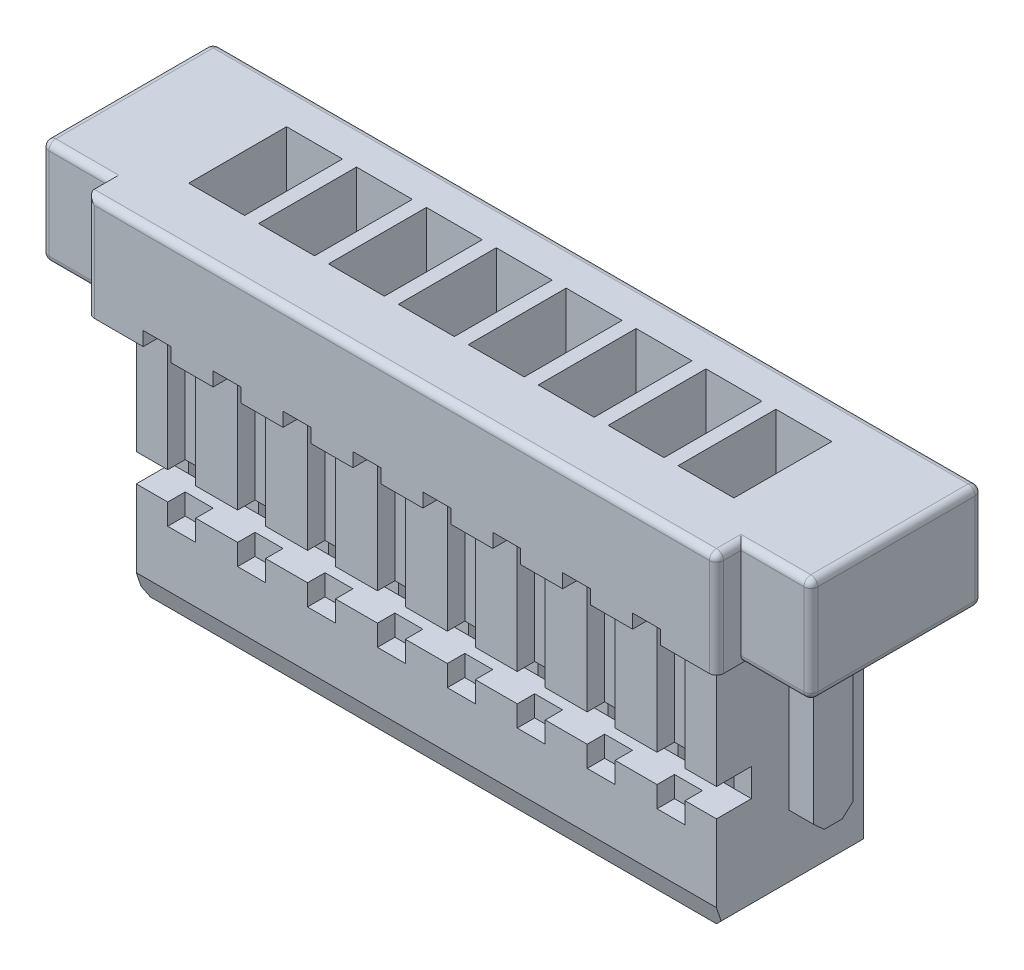
SolidWorks part; units mm, degrees
ref_plane "Front" through (0, 0, 0) normal (0, 0, 1) x (1, 0, 0)
ref_plane "Top" through (0, 0, 0) normal (0, 1, 0) x (1, 0, 0)
ref_plane "Right" through (0, 0, 0) normal (1, 0, 0) x (0, 0, -1)
sketch "Sketch1" plane through (0, 0, 0) normal (0, 0, 1) x (1, 0, 0)
  line L0 (-5.5, 1) -> (-4.5, 1)
  line L1 (5.5, 2.5) -> (-5.5, 2.5)
  line L2 (5.5, 2.5) -> (5.5, 1)
  line L3 (4.5, -2.5) -> (-4.5, -2.5)
  line L4 (-5.5, 2.5) -> (-5.5, 1)
  line L7 (-4.5, 1) -> (-4.5, -2.5)
  line L8 (0, 2.2875) -> (0, 41.3139) construction
  line L9 (4.5, 1) -> (4.5, -2.5)
  line L10 (5.5, 1) -> (4.5, 1)
  point P0 (0, 0)
  dimension "D1" = 11
  dimension "D2" = 5
  dimension "D3" = 9
  dimension "D4" = 1.5
extrude "Extrude1" add sketch "Sketch1" along normal blind 2.8
sketch "Sketch2" plane through (0, 0, 0) normal (1, 0, 0) x (0, 0, -1)
  line L0 (-2.45, 1) -> (-2.45, -2.5)
  line L1 (-0.35, 1) -> (-0.35, -2.5)
  line L2 (0, -2.5) -> (0, 1) construction
  line L3 (-2.8, -2.5) -> (-2.8, 1) construction
  line L4 (-2.8, -2.5) -> (0, -2.5) construction
  line L5 (-2.8, 1) -> (0, 1) construction
  line L6 (0, -2.5) -> (0, 1)
  line L7 (-2.8, -2.5) -> (-2.8, 1)
  line L8 (-2.8, -2.5) -> (-2.45, -2.5)
  line L9 (-2.8, 1) -> (-2.45, 1)
  line L10 (-0.35, 1) -> (0, 1)
  line L11 (-0.35, -2.5) -> (0, -2.5)
  dimension "D1" = 2.1
  dimension "D2" = 0.35
extrude "Extrude2" cut sketch "Sketch2" against normal through all and the other way through all
sketch "Sketch3" plane through (5.5, 0, 0) normal (1, 0, 0) x (0, 0, -1)
  line L0 (-2.45, 1) -> (-2.45, 2.5)
  line L1 (-2.8, 1) -> (0, 1) construction
  line L2 (-2.45, 1) -> (-0.35, 1) construction
  line L3 (-2.8, 2.5) -> (0, 2.5) construction
  line L4 (-2.8, 1) -> (-2.8, 2.5) construction
  line L5 (-2.8, 1) -> (-2.45, 1)
  line L6 (-2.8, 1) -> (-2.8, 2.5)
  line L7 (-2.8, 2.5) -> (-2.45, 2.5)
extrude "Extrude3" cut sketch "Sketch3" along direction (-1, 0, 0) on the side against the normal blind 1
mirror "Mirror1" about plane through (0, 0, 0) normal (1, 0, 0) of "Extrude3"
sketch "Sketch4" plane through (4.5, 0, 0) normal (1, 0, 0) x (0, 0, -1)
  line L0 (-1.41, 1) -> (-1.41, -1.5131)
  line L1 (-2.45, 1) -> (0, 1) construction
  line L2 (-1.41, -1.5131) -> (-1.26, -1.65)
  line L3 (-1.26, -1.65) -> (-1, -1.65)
  line L4 (-1, -1.65) -> (-0.85, -1.5131)
  line L5 (-0.85, -1.5131) -> (-0.85, 1)
  line L6 (-2.45, 1) -> (-0.35, 1) construction
  line L7 (-0.85, 1) -> (-0.35, 1)
  line L8 (-0.35, -2.5) -> (-0.35, 1) construction
  line L9 (-2.45, -2.5) -> (-0.35, -2.5) construction
  line L10 (-2.45, 1) -> (-2.45, -2.5) construction
  line L11 (-0.35, -2.5) -> (-0.35, 1)
  line L12 (-2.45, -2.5) -> (-0.35, -2.5)
  line L13 (-2.45, 1) -> (-2.45, -2.5)
  line L14 (-2.45, 1) -> (-1.41, 1)
  line L15 (0, 1) -> (0, 2.5) construction
  dimension "D1" = 0.85
  dimension "D2" = 0.56
  dimension "D3" = 0.85
  dimension "D4" = 0.15
  dimension "D5" = 0.15
extrude "Extrude4" cut sketch "Sketch4" against normal blind 0.35
mirror "Mirror2" about plane through (0, 0, 0) normal (1, 0, 0) of "Extrude4"
sketch "Sketch5" plane through (4.15, 0, 0) normal (1, 0, 0) x (0, 0, -1)
  line L0 (-2.45, -0.7) -> (-1.95, -0.7)
  line L1 (-1.95, -0.7) -> (-1.95, -1.1)
  line L2 (-1.95, -1.1) -> (-2.45, -1.1)
  line L3 (-2.45, 1) -> (-2.45, -2.5) construction
  line L4 (-2.45, -0.7) -> (-2.45, -1.1)
  line L5 (-2.45, -2.5) -> (-0.35, -2.5) construction
  dimension "D1" = 0.4
  dimension "D2" = 1.4
  dimension "D3" = 0.5
extrude "Extrude5" cut sketch "Sketch5" against normal through all
sketch "Sketch6" plane through (0, 2.5, 0) normal (0, 1, 0) x (1, 0, 0)
  line L0 (0, 2.2819) -> (0, -4.8491) construction
  line L1 (5.5, 0) -> (-5.5, 0) construction
  line L2 (-3.9, -1.95) -> (-3.1, -1.95)
  line L3 (-3.9, -1.95) -> (-3.9, -0.55)
  line L4 (-3.9, -0.55) -> (-3.1, -0.55)
  line L5 (-3.1, -1.95) -> (-3.1, -0.55)
  line L6 (-3.5, -0.55) -> (-3.5, -3.8689) construction
  dimension "D1" = 0.8
  dimension "D2" = 1.4
  dimension "D3" = 0.55
  dimension "D4" = 3.5
extrude "Extrude6" cut sketch "Sketch6" against normal blind 4.5
pattern_linear "LPattern1" count 8 spacing 1 along (1, 0, 0) of "Extrude6"
sketch "Sketch7" plane through (0, 0, 2.8) normal (0, 0, 1) x (1, 0, 0)
  line L0 (-3.5, -1.1) -> (-3.5, 3.4491) construction
  line L3 (-4.15, -1.1) -> (4.15, -1.1) construction
  line L5 (-3.7, -1.4) -> (-3.3, -1.4)
  line L6 (-3.7, -1.4) -> (-3.7, 1.2)
  line L8 (-3.3, -1.4) -> (-3.3, 1.2)
  line L10 (-3.7, 1.2) -> (-3.3, 1.2)
  line L11 (4.5, 2.5) -> (-4.5, 2.5) construction
  dimension "D1" = 3.5
  dimension "D2" = 0.4
  dimension "D3" = 0.2
  dimension "D5" = 1.3
extrude "Extrude7" cut sketch "Sketch7" against normal blind 0.6
pattern_linear "LPattern2" count 8 spacing 1 along (1, 0, 0) of "Extrude7"
sketch "Sketch9" plane through (0, 0, 0) normal (0, 0, -1) x (-1, 0, 0)
  line L0 (-3.75, 1) -> (-3.75, 1.5)
  line L1 (4.15, 1) -> (-4.15, 1) construction
  line L2 (-3.75, 1.5) -> (-3.25, 1.5)
  line L3 (-3.25, 1.5) -> (-3.25, 1)
  line L4 (-3.5, 1.5) -> (-3.5, 0.2625) construction
  line L5 (-3.25, 1) -> (-3.75, 1)
  line L6 (-5.5, 2.5) -> (5.5, 2.5) construction
  dimension "D1" = 0.5
  dimension "D2" = 1
  dimension "D3" = 3.5
extrude "Extrude9" cut sketch "Sketch9" against normal up to surface (0.35 mm away) up to face at (0, -0.75, 0.35)
pattern_linear "LPattern3" count 8 spacing 1 along (-1, 0, 0) of "Extrude9"
sketch "Sketch10" plane through (0, -2.5, 0) normal (0, -1, 0) x (1, 0, 0)
  line L0 (-3.5, 0.65) -> (-3.5, 3.7831) construction
  line L1 (-3.675, 0.65) -> (-3.325, 0.65)
  line L2 (-3.675, 0.65) -> (-3.675, 1.4)
  line L3 (-3.675, 1.4) -> (-3.325, 1.4)
  line L4 (-3.325, 0.65) -> (-3.325, 1.4)
  line L6 (-4.15, 0.35) -> (4.15, 0.35) construction
  dimension "D1" = 3.5
  dimension "D2" = 0.35
  dimension "D3" = 0.75
  dimension "D4" = 0.3
extrude "Extrude10" cut sketch "Sketch10" against normal through all
pattern_linear "LPattern4" count 8 spacing 1 along (1, 0, 0) of "Extrude10"
fillet "Fillet1" radius 0.1 19 edges at (0, 2.5, 0) (5.5, 1.75, 0) (4.625, 1, 0) (0, 2.5, 2.8) (5.5, 1, 1.225) (5.5, 2.5, 1.225) (5, 1, 2.45) (4.5, 1.75, 2.8) (4.5, 2.5, 2.625) (5, 2.5, 2.45) (5.5, 1.75, 2.45) (-4.625, 1, 0) (-5.5, 1, 1.225) (-5.5, 2.5, 1.225) (-5.5, 1.75, 2.45) (-5, 1, 2.45) (-5, 2.5, 2.45) (-4.5, 1.75, 2.8) (-5.5, 1.75, 0)
chamfer "Chamfer1" distance 0.1 distance2 0.3 1 edges at (0, -2.5, 2.45)
chamfer "Chamfer2" distance 0.1 angle 45 3 edges at (-4.15, -2.5, 1.35) (0, -2.5, 0.35) (4.15, -2.5, 1.35)
